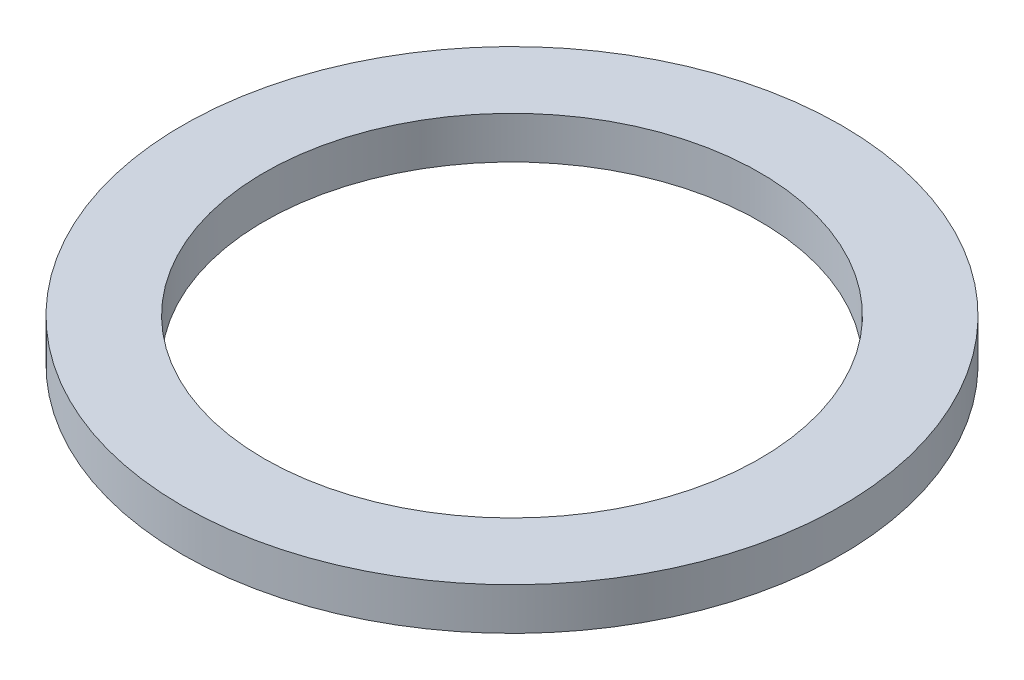
SolidWorks part; units mm, degrees
ref_plane "Front Plane" through (0, 0, 0) normal (0, 0, 1) x (1, 0, 0)
ref_plane "Top Plane" through (0, 0, 0) normal (0, 1, 0) x (1, 0, 0)
ref_plane "Right Plane" through (0, 0, 0) normal (1, 0, 0) x (0, 0, -1)
sketch "Sketch1" plane through (0, 0, 0) normal (0, 1, 0) x (1, 0, 0)
  circle A0 centre (0, 0) radius 2.3876
  circle A1 centre (0, 0) radius 3.175
  dimension "D1" = 4.7752
  dimension "D2" = 6.35
extrude "Boss-Extrude1" add sketch "Sketch1" along normal blind 0.4064
